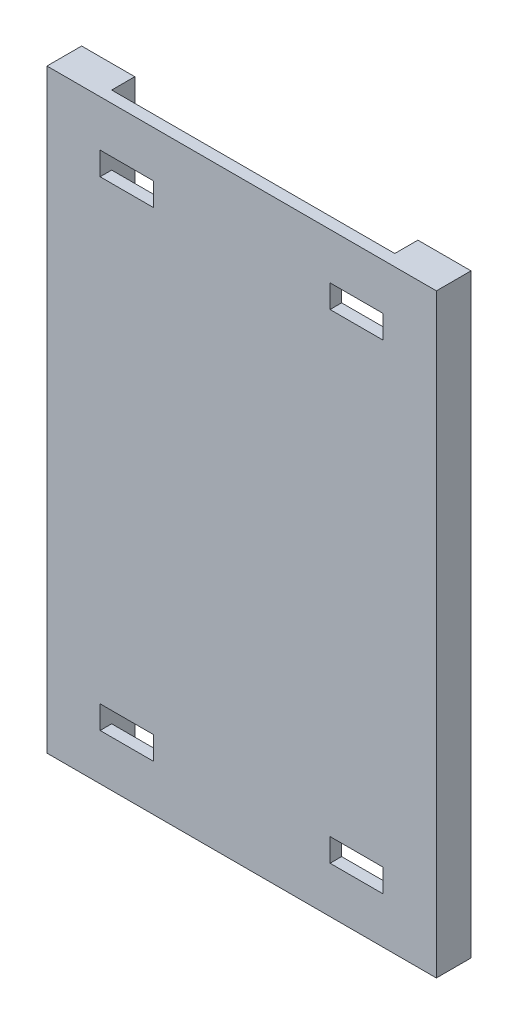
SolidWorks part; units mm, degrees
material "Pine"
ref_plane "Front Plane" through (0, 0, 0) normal (0, 0, 1) x (1, 0, 0)
ref_plane "Top Plane" through (0, 0, 0) normal (0, 1, 0) x (1, 0, 0)
ref_plane "Right Plane" through (0, 0, 0) normal (1, 0, 0) x (0, 0, -1)
sketch "Sketch1" plane through (0, 0, 0) normal (0, 0, 1) x (1, 0, 0)
  line L0 (-176, -425) -> (-176, -405) construction
  line L1 (-176, -405) -> (-222, -405) construction
  line L2 (-222, -405) -> (-222, -425) construction
  line L3 (-222, -425) -> (-176, -425) construction
  line L4 (23, -425) -> (23, -405) construction
  line L5 (23, -405) -> (-23, -405) construction
  line L6 (-23, -405) -> (-23, -425) construction
  line L7 (-23, -425) -> (23, -425) construction
  line L8 (-222, 10) -> (-222, -10) construction
  line L9 (-222, -10) -> (-176, -10) construction
  line L10 (-176, -10) -> (-176, 10) construction
  line L11 (-176, 10) -> (-222, 10) construction
  line L12 (-23, 10) -> (-23, -10) construction
  line L13 (-23, -10) -> (23, -10) construction
  line L14 (23, -10) -> (23, 10) construction
  line L15 (23, 10) -> (-23, 10) construction
  line L16 (-176, -425) -> (-176, -405)
  line L17 (-176, -405) -> (-222, -405)
  line L18 (-222, -405) -> (-222, -425)
  line L19 (-222, -425) -> (-176, -425)
  line L20 (23, -425) -> (23, -405)
  line L21 (23, -405) -> (-23, -405)
  line L22 (-23, -405) -> (-23, -425)
  line L23 (-23, -425) -> (23, -425)
  line L24 (-222, 10) -> (-222, -10)
  line L25 (-222, -10) -> (-176, -10)
  line L26 (-176, -10) -> (-176, 10)
  line L27 (-176, 10) -> (-222, 10)
  line L28 (-23, 10) -> (-23, -10)
  line L29 (-23, -10) -> (23, -10)
  line L30 (23, -10) -> (23, 10)
  line L31 (23, 10) -> (-23, 10)
  line L33 (69, 50) -> (-268, 50)
  line L34 (69, 50) -> (69, -465)
  line L35 (69, -465) -> (-268, -465)
  line L36 (-268, 50) -> (-268, -465)
  dimension "D1" = 46
  dimension "D2" = 40
  dimension "D3" = 40
  dimension "D4" = 46
extrude "Boss-Extrude1" add sketch "Sketch1" against normal blind 10
sketch "Sketch2" plane through (0, 0, -10) normal (0, 0, -1) x (-1, 0, 0)
  line L0 (-69, 50) -> (268, 50) construction
  line L1 (268, -465) -> (222, -465)
  line L2 (268, -465) -> (268, 50)
  line L3 (268, 50) -> (222, 50)
  line L4 (222, -465) -> (222, 50)
  line L5 (222, 10) -> (222, -10) construction
  line L6 (-23, -10) -> (-23, 10) construction
  line L7 (-69, -465) -> (-23, -465)
  line L8 (-69, -465) -> (-69, 50)
  line L9 (-69, 50) -> (-23, 50)
  line L10 (-23, -465) -> (-23, 50)
extrude "Boss-Extrude2" add sketch "Sketch2" along normal blind 20
